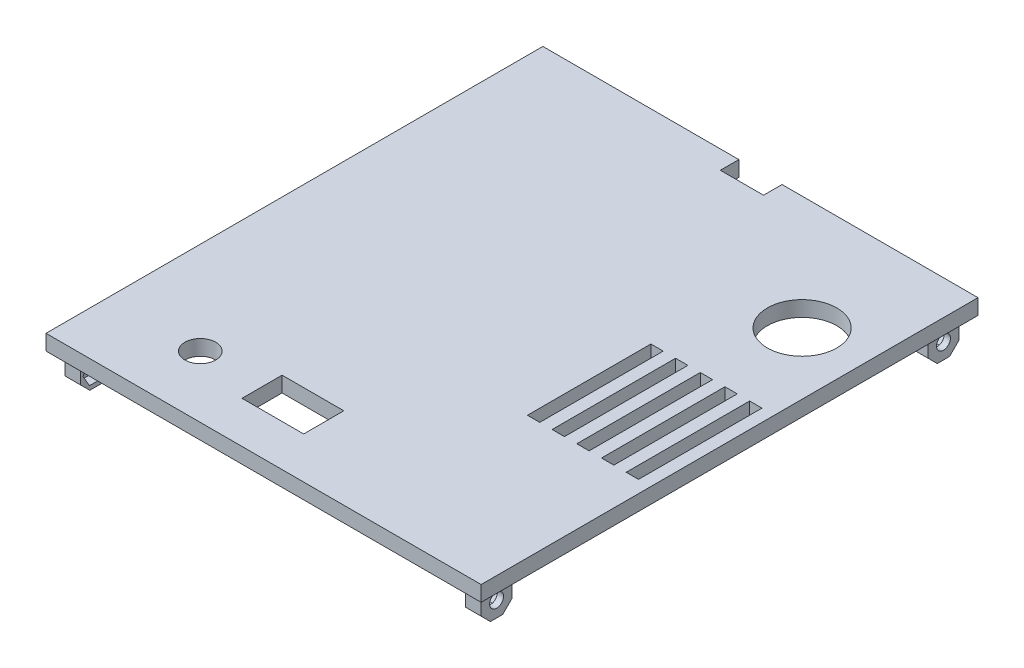
SolidWorks part; units mm, degrees
ref_plane "Front Plane" through (0, 0, 0) normal (0, 0, 1) x (1, 0, 0)
ref_plane "Top Plane" through (0, 0, 0) normal (0, 1, 0) x (1, 0, 0)
ref_plane "Right Plane" through (0, 0, 0) normal (1, 0, 0) x (0, 0, -1)
sketch "Sketch1" plane through (0, 0, 0) normal (0, 1, 0) x (1, 0, 0)
  line L1 (-70.5, -80.5) -> (70.5, -80.5)
  line L2 (-70.5, -80.5) -> (-70.5, 80.5)
  line L3 (-70.5, 80.5) -> (70.5, 80.5)
  line L4 (70.5, -80.5) -> (70.5, 80.5)
  line L5 (-70.5, -80.5) -> (70.5, 80.5) construction
  line L6 (-70.5, 80.5) -> (70.5, -80.5) construction
  point P0 (0, 0)
  dimension "D1" = 141
  dimension "D2" = 161
extrude "Boss-Extrude1" add sketch "Sketch1" along normal blind 5
sketch "Sketch2" plane through (0, 5, 0) normal (0, 1, 0) x (1, 0, 0)
  line L0 (70.5, 80.5) -> (-70.5, 80.5) construction
  line L1 (70.5, -80.5) -> (70.5, 80.5) construction
  circle A0 centre (50.5, 43.5) radius 11.25
  dimension "D1" = 37
  dimension "D2" = 20
  dimension "D3" = 22.5
extrude "Cut-Extrude1" cut sketch "Sketch2" against normal up to next and the other way through all
sketch "Sketch3" plane through (0, 5, 0) normal (0, 1, 0) x (1, 0, 0)
  line L0 (66.5, -25.5) -> (26.5, -25.5) construction
  line L1 (26.5, -25.5) -> (26.5, 14.5) construction
  line L2 (26.5, 14.5) -> (66.5, 14.5) construction
  line L3 (66.5, 14.5) -> (66.5, -25.5) construction
  line L4 (-70.5, -80.5) -> (70.5, -80.5) construction
  line L5 (70.5, -80.5) -> (70.5, 80.5) construction
  line L6 (26.5, -5.5) -> (66.5, -5.5) construction
  line L7 (46.5, 14.5) -> (46.5, -25.5) construction
  line L8 (38.5, -25.5) -> (38.5, 14.5)
  line L9 (30.5, -25.5) -> (34.5, -25.5)
  line L10 (30.5, -25.5) -> (30.5, 14.5)
  line L11 (30.5, 14.5) -> (34.5, 14.5)
  line L12 (34.5, -25.5) -> (34.5, 14.5)
  line L13 (30.5, -25.5) -> (34.5, 14.5) construction
  line L14 (30.5, 14.5) -> (34.5, -25.5) construction
  line L15 (38.5, -25.5) -> (42.5, -25.5)
  line L16 (42.5, -25.5) -> (42.5, 14.5)
  line L17 (38.5, 14.5) -> (42.5, 14.5)
  line L18 (46.5, -25.5) -> (46.5, 14.5)
  line L19 (46.5, -25.5) -> (50.5, -25.5)
  line L20 (50.5, -25.5) -> (50.5, 14.5)
  line L21 (46.5, 14.5) -> (50.5, 14.5)
  line L22 (54.5, -25.5) -> (54.5, 14.5)
  line L23 (54.5, -25.5) -> (58.5, -25.5)
  line L24 (58.5, -25.5) -> (58.5, 14.5)
  line L25 (54.5, 14.5) -> (58.5, 14.5)
  line L26 (62.5, -25.5) -> (62.5, 14.5)
  line L27 (62.5, -25.5) -> (66.5, -25.5)
  line L28 (66.5, -25.5) -> (66.5, 14.5)
  line L29 (62.5, 14.5) -> (66.5, 14.5)
  point P12 (32.5, -5.5)
  dimension "D5" = 4
  dimension "D6" = 4
  dimension "D7" = 5
  dimension "D8" = 4
  dimension "D1" = 40
  dimension "D2" = 40
  dimension "D3" = 55
  dimension "D4" = 4
extrude "Cut-Extrude2" cut sketch "Sketch3" against normal up to next
sketch "Sketch4" plane through (0, 0, 0) normal (0, -1, 0) x (1, 0, 0)
  line L0 (70.5, 80.5) -> (70.5, -80.5) construction
  line L1 (62.4, 77.4) -> (67.4, 77.4)
  line L2 (62.4, 77.4) -> (62.4, 67.4)
  line L3 (62.4, 67.4) -> (67.4, 67.4)
  line L4 (67.4, 77.4) -> (67.4, 67.4)
  line L5 (-70.5, 80.5) -> (70.5, 80.5) construction
  line L6 (0, 80.5) -> (0, -80.5) construction
  line L7 (70.5, -80.5) -> (-70.5, -80.5) construction
  line L8 (-70.5, 0) -> (70.5, 0) construction
  line L9 (-70.5, -80.5) -> (-70.5, 80.5) construction
  line L10 (-62.4, 67.4) -> (-67.4, 67.4)
  line L11 (-67.4, 77.4) -> (-67.4, 67.4)
  line L12 (-62.4, 77.4) -> (-67.4, 77.4)
  line L13 (-62.4, 77.4) -> (-62.4, 67.4)
  line L14 (62.4, -67.4) -> (67.4, -67.4)
  line L15 (67.4, -77.4) -> (67.4, -67.4)
  line L16 (62.4, -77.4) -> (67.4, -77.4)
  line L17 (62.4, -77.4) -> (62.4, -67.4)
  line L18 (-62.4, -77.4) -> (-62.4, -67.4)
  line L19 (-62.4, -77.4) -> (-67.4, -77.4)
  line L20 (-67.4, -77.4) -> (-67.4, -67.4)
  line L21 (-62.4, -67.4) -> (-67.4, -67.4)
  dimension "D1" = 3.1
  dimension "D2" = 3.1
  dimension "D3" = 5
  dimension "D4" = 10
extrude "Boss-Extrude2" add sketch "Sketch4" along normal blind 10
sketch "Sketch5" plane through (67.4, 0, 0) normal (1, 0, 0) x (0, 0, -1)
  line L0 (0, 0) -> (0, 5) construction
  line L1 (-80.5, 0) -> (80.5, 0) construction
  line L2 (-80.5, 5) -> (80.5, 5) construction
  line L3 (-77.4, -5) -> (-67.4, -5) construction
  line L4 (-77.4, -10) -> (-77.4, 0) construction
  line L5 (-67.4, -10) -> (-67.4, 0) construction
  circle A0 centre (-72.4, -5) radius 2.25
  circle A1 centre (72.4, -5) radius 2.25
  dimension "D1" = 4.5
extrude "Cut-Extrude3" cut sketch "Sketch5" against normal through all and the other way through all
sketch "Sketch6" plane through (-62.4, 0, 0) normal (1, 0, 0) x (0, 0, -1)
  line L1 (-68.1853, -5) -> (-70.2927, -1.35)
  line L2 (-70.2927, -1.35) -> (-74.5073, -1.35)
  line L3 (-74.5073, -1.35) -> (-76.6147, -5)
  line L4 (-76.6147, -5) -> (-74.5073, -8.65)
  line L5 (-74.5073, -8.65) -> (-70.2927, -8.65)
  line L6 (-70.2927, -8.65) -> (-68.1853, -5)
  circle A0 centre (-72.4, -5) radius 3.65 construction
  dimension "D1" = 7.3
  dimension "D2" = 3.65
extrude "Cut-Extrude4" cut sketch "Sketch6" against normal blind 3
chamfer "Chamfer1" distance 3 angle 45 8 edges at (-64.9, -10, 67.4) (-64.9, -10, 77.4) (64.9, -10, -77.4) (64.9, -10, -67.4) (-64.9, -10, -77.4) (-64.9, -10, -67.4) (64.9, -10, 67.4) (64.9, -10, 77.4)
mirror "Mirror3" about plane through (0, 0, 0) normal (1, 0, 0) of "Cut-Extrude4"
mirror "Mirror4" about plane through (0, 0, 0) normal (0, 0, 1) of "Cut-Extrude4", "Mirror3"
sketch "Sketch7" plane through (0, 5, 0) normal (0, 1, 0) x (1, 0, 0)
  line L0 (-70.5, -60.5) -> (70.5, -60.5) construction
  line L5 (-70.5, 80.5) -> (-70.5, -80.5) construction
  line L6 (70.5, -80.5) -> (70.5, 80.5) construction
  line L7 (-70.5, -80.5) -> (70.5, -80.5) construction
  line L9 (-20.5, -67) -> (-0.5, -67)
  line L10 (-20.5, -67) -> (-20.5, -54)
  line L11 (-20.5, -54) -> (-0.5, -54)
  line L12 (-0.5, -67) -> (-0.5, -54)
  line L13 (-20.5, -67) -> (-0.5, -54) construction
  line L14 (-20.5, -54) -> (-0.5, -67) construction
  circle A0 centre (-40.5, -60.5) radius 5
  point P8 (-10.5, -60.5)
  dimension "D4" = 10
  dimension "D5" = 30
  dimension "D6" = 30
  dimension "D1" = 20
  dimension "D2" = 20
  dimension "D3" = 13
extrude "Cut-Extrude5" cut sketch "Sketch7" against normal up to next and the other way through all
sketch "Sketch8" plane through (0, 0, 0) normal (0, -1, 0) x (1, 0, 0)
  line L0 (-40.5, 60.5) -> (-40.5, 74.5) construction
  line L1 (-45.5, 60.5) -> (-35.5, 60.5) construction
  line L2 (-42.25, 73.5) -> (-38.75, 73.5)
  line L3 (-42.25, 73.5) -> (-42.25, 74.5)
  line L4 (-42.25, 74.5) -> (-38.75, 74.5)
  line L5 (-38.75, 73.5) -> (-38.75, 74.5)
  line L6 (-42.25, 73.5) -> (-38.75, 74.5) construction
  line L7 (-42.25, 74.5) -> (-38.75, 73.5) construction
  line L8 (-42.25, 46.5) -> (-38.75, 46.5)
  line L9 (-38.75, 47.5) -> (-38.75, 46.5)
  line L10 (-42.25, 47.5) -> (-38.75, 47.5)
  line L11 (-42.25, 47.5) -> (-42.25, 46.5)
  circle A0 centre (-40.5, 60.5) radius 5 construction
  point P3 (-40.5, 74)
  dimension "D1" = 14
  dimension "D2" = 1
  dimension "D3" = 0.5
  dimension "D4" = 3.5
extrude "Cut-Extrude6" cut sketch "Sketch8" against normal blind 4 and the other way through all
sketch "Sketch9" plane through (0, 5, 0) normal (0, 1, 0) x (1, 0, 0)
  line L0 (0, 0) -> (0, 80.5) construction
  line L1 (70.5, 80.5) -> (-70.5, 80.5) construction
  line L3 (-7, 74.5) -> (7, 74.5)
  line L4 (-7, 74.5) -> (-7, 80.5)
  line L5 (-7, 80.5) -> (7, 80.5)
  line L6 (7, 74.5) -> (7, 80.5)
  line L7 (-7, 74.5) -> (7, 80.5) construction
  line L8 (-7, 80.5) -> (7, 74.5) construction
  point P5 (0, 77.5)
  dimension "D1" = 6
  dimension "D2" = 14
extrude "Cut-Extrude7" cut sketch "Sketch9" against normal up to next and the other way through all
